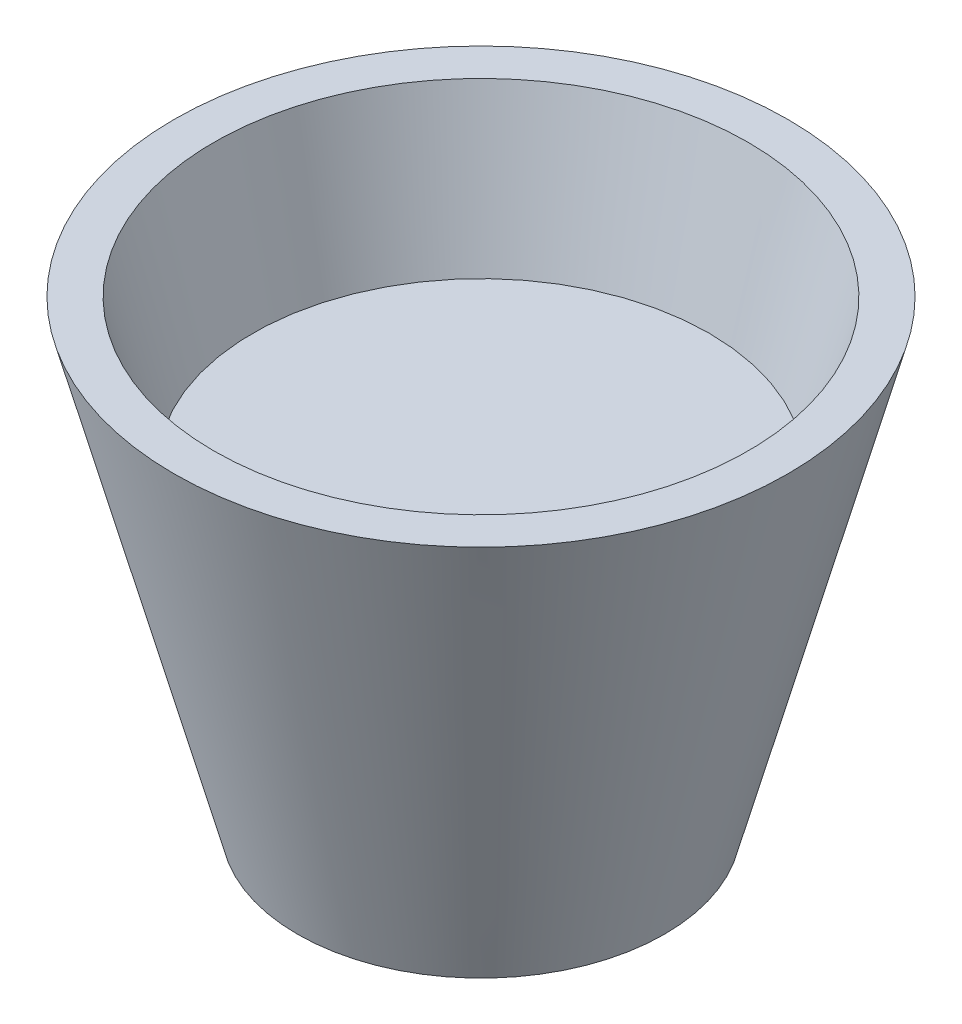
SolidWorks part; units mm, degrees
ref_plane "Front Plane" through (0, 0, 0) normal (0, 0, 1) x (1, 0, 0)
ref_plane "Top Plane" through (0, 0, 0) normal (0, 1, 0) x (1, 0, 0)
ref_plane "Right Plane" through (0, 0, 0) normal (1, 0, 0) x (0, 0, -1)
sketch "Sketch1" plane through (0, 0, 0) normal (0, 0, 1) x (1, 0, 0)
  line L0 (0, 0) -> (25.5097, 0)
  line L1 (25.5097, 0) -> (44.226, 69.85)
  line L2 (44.226, 69.85) -> (50.8, 69.85)
  line L3 (50.8, 69.85) -> (30.3823, -6.35)
  line L4 (30.3823, -6.35) -> (0, -6.35)
  line L5 (0, 0) -> (0, -6.35)
  line L6 (0, 0) -> (0, 90.5749) construction
  dimension "D1" = 75
  dimension "D2" = 6.35
  dimension "D3" = 6.35
  dimension "D4" = 76.2
  dimension "D5" = 50.8
revolve "Revolve1" add sketch "Sketch1" angle 360 about L6
sketch "Sketch2" plane through (0, 0, 0) normal (0, 0, 1) x (1, 0, 0)
  line L0 (0, 0) -> (25.5229, 0)
  line L1 (25.5229, 0) -> (37.931, 45.7287)
  line L2 (37.931, 45.7287) -> (0, 45.7287)
  line L3 (0, 45.7287) -> (0, 0)
  line L4 (0, 0) -> (0, 63.7911) construction
revolve "Revolve2" add sketch "Sketch2" angle 360 about L4
